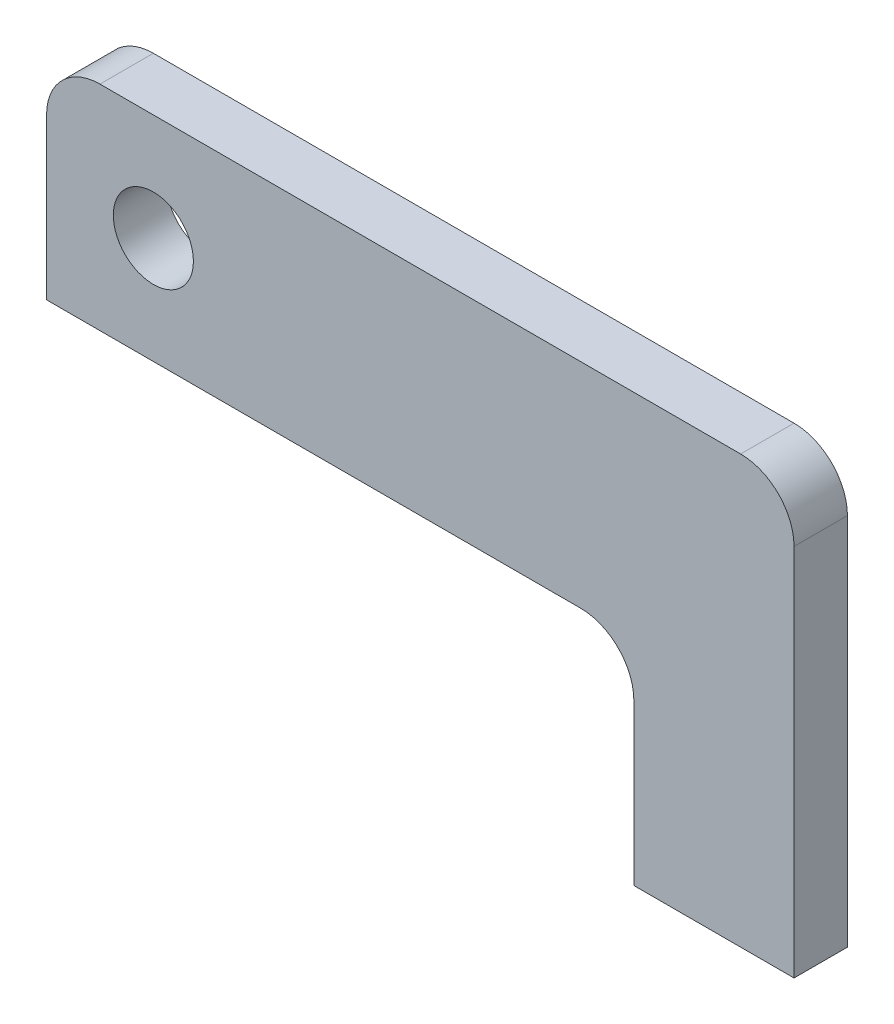
SolidWorks part; units mm, degrees
ref_plane "Front Plane" through (0, 0, 0) normal (0, 0, 1) x (1, 0, 0)
ref_plane "Top Plane" through (0, 0, 0) normal (0, 1, 0) x (1, 0, 0)
ref_plane "Right Plane" through (0, 0, 0) normal (1, 0, 0) x (0, 0, -1)
sketch "Sketch4" plane through (0, 0, 0) normal (0, 0, 1) x (1, 0, 0)
  line L0 (0, 0) -> (0, 19.05)
  line L1 (6.35, 25.4) -> (82.55, 25.4)
  line L2 (88.9, 19.05) -> (88.9, -25.4)
  line L3 (88.9, -25.4) -> (69.85, -25.4)
  line L4 (69.85, -25.4) -> (69.85, -6.35)
  line L7 (63.5, 0) -> (0, 0)
  line L8 (25.4, 25.4) -> (25.4, 0) construction
  arc A0 (82.55, 25.4) -> (88.9, 19.05) centre (82.55, 19.05) cw
  arc A1 (69.85, -6.35) -> (63.5, 0) centre (63.5, -6.35) ccw
  arc A2 (0, 19.05) -> (6.35, 25.4) centre (6.35, 19.05) cw
  circle A3 centre (12.7, 12.7) radius 4.7625
  point P11 (88.9, 25.4)
  point P17 (0, 25.4)
  dimension "D7" = 6.35
  dimension "D6" = 38.1
  dimension "D5" = 9.525
  dimension "D1" = 25.4
  dimension "D2" = 50.8
  dimension "D3" = 44.45
  dimension "D4" = 19.05
  dimension "D8" = 12.7
  dimension "D9" = 12.7
  dimension "D10" = 12.7
  dimension "D11" = 63.5
extrude "Boss-Extrude2" add sketch "Sketch4" along normal blind 6.35 contours L8 L1 A2 L0 L7 A3 | L1 L8 L7 A1 L4 L3 L2 A0
